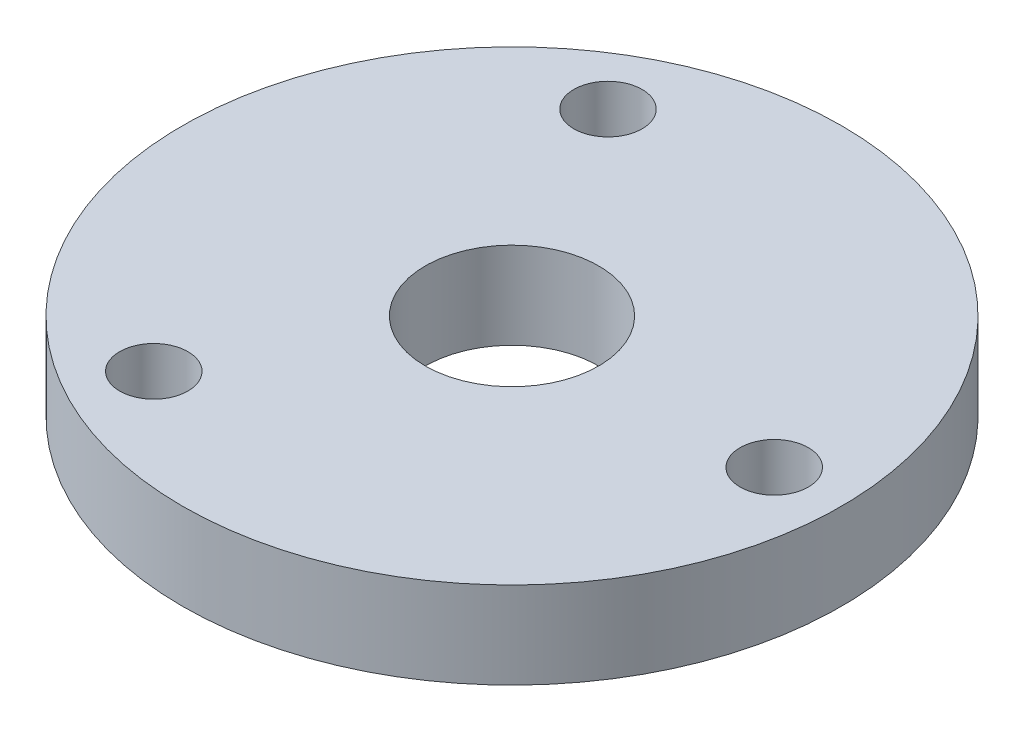
SolidWorks part; units mm, degrees
material "ABS"
ref_plane "Front Plane" through (0, 0, 0) normal (0, 0, 1) x (1, 0, 0)
ref_plane "Top Plane" through (0, 0, 0) normal (0, 1, 0) x (1, 0, 0)
ref_plane "Right Plane" through (0, 0, 0) normal (1, 0, 0) x (0, 0, -1)
sketch "Sketch1" plane through (0, 0, 0) normal (0, 1, 0) x (1, 0, 0)
  line L0 (13, 0) -> (25.4, 0) construction
  line L2 (19.2, 0) -> (9.6, 16.6277) construction
  line L3 (9.6, 16.6277) -> (-9.6, 16.6277) construction
  line L4 (-9.6, 16.6277) -> (-19.2, 0) construction
  line L5 (-19.2, 0) -> (-9.6, -16.6277) construction
  line L6 (-9.6, -16.6277) -> (9.6, -16.6277) construction
  line L7 (9.6, -16.6277) -> (19.2, 0) construction
  circle A0 centre (0, 0) radius 24.13
  circle A1 centre (0, 0) radius 25.4 construction
  circle A2 centre (0, 0) radius 13 construction
  circle A3 centre (19.2, 0) radius 2.5
  circle A4 centre (0, 0) radius 16.6277 construction
  circle A5 centre (-9.6, 16.6277) radius 2.5
  circle A6 centre (-9.6, -16.6277) radius 2.5
  circle A7 centre (0, 0) radius 6.35
  dimension "D1" = 48.26
  dimension "D2" = 50.8
  dimension "D3" = 26
  dimension "D4" = 5
  dimension "D5" = 5
  dimension "D6" = 5
  dimension "D7" = 12.7
extrude "Boss-Extrude1" add sketch "Sketch1" along normal blind 6.35
sketch "Sketch2" plane through (0, 6.35, 0) normal (0, 1, 0) x (1, 0, 0)
  line L1 (9.525, 0) -> (4.7625, 8.2489)
  line L2 (4.7625, 8.2489) -> (-4.7625, 8.2489)
  line L3 (-4.7625, 8.2489) -> (-9.525, 0)
  line L4 (-9.525, 0) -> (-4.7625, -8.2489)
  line L5 (-4.7625, -8.2489) -> (4.7625, -8.2489)
  line L6 (4.7625, -8.2489) -> (9.525, 0)
  circle A0 centre (0, 0) radius 8.2489 construction
  dimension "D1" = 9.525
